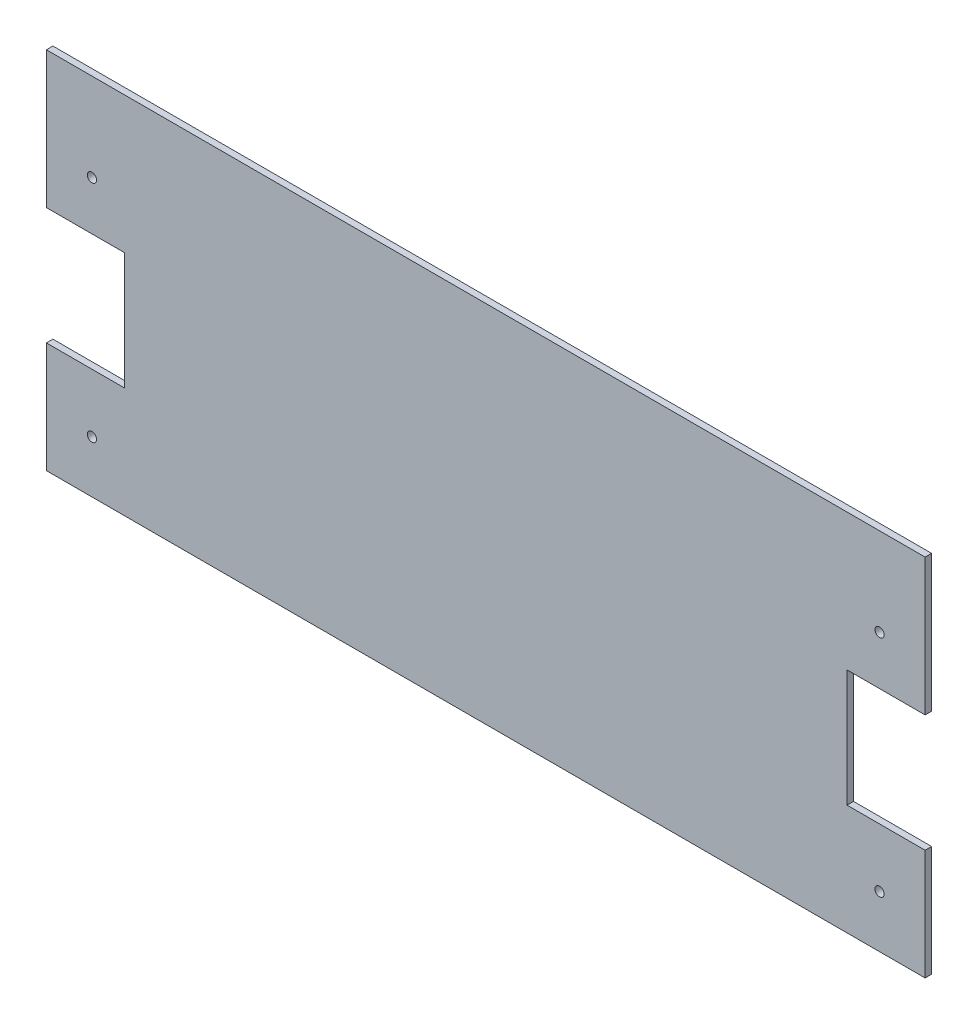
SolidWorks part; units mm, degrees
ref_plane "Front Plane" through (0, 0, 0) normal (0, 0, 1) x (1, 0, 0)
ref_plane "Top Plane" through (0, 0, 0) normal (0, 1, 0) x (1, 0, 0)
ref_plane "Right Plane" through (0, 0, 0) normal (1, 0, 0) x (0, 0, -1)
sketch "Sketch1" plane through (0, 0, 0) normal (0, 0, 1) x (1, 0, 0)
  line L0 (0, 88.9) -> (0, -88.9) construction
  line L1 (-214.3125, -88.9) -> (214.3125, -88.9)
  line L2 (-214.3125, -88.9) -> (-214.3125, 88.9)
  line L3 (-214.3125, 88.9) -> (214.3125, 88.9)
  line L4 (214.3125, -88.9) -> (214.3125, 88.9)
  line L5 (-214.3125, -88.9) -> (214.3125, 88.9) construction
  line L6 (-214.3125, 88.9) -> (214.3125, -88.9) construction
  line L7 (-214.3125, -34.925) -> (-176.2125, -34.925)
  line L8 (-214.3125, -34.925) -> (-214.3125, 22.225)
  line L9 (-214.3125, 22.225) -> (-176.2125, 22.225)
  line L10 (-176.2125, -34.925) -> (-176.2125, 22.225)
  line L11 (214.3125, 22.225) -> (176.2125, 22.225)
  line L12 (176.2125, -34.925) -> (176.2125, 22.225)
  line L13 (214.3125, -34.925) -> (176.2125, -34.925)
  line L14 (214.3125, -34.925) -> (214.3125, 22.225)
  circle A0 centre (-192.0875, 46.0375) radius 2.25
  circle A1 centre (-192.0875, -63.5) radius 2.25
  circle A2 centre (192.0875, -63.5) radius 2.25
  circle A3 centre (192.0875, 46.0375) radius 2.25
  point P0 (0, 0)
  dimension "D3" = 4.5
  dimension "D4" = 4.5
  dimension "D7" = 42.8625
  dimension "D1" = 428.625
  dimension "D2" = 177.8
  dimension "D5" = 22.225
  dimension "D6" = 22.225
  dimension "D8" = 152.4
  dimension "D9" = 66.675
  dimension "D10" = 123.825
  dimension "D11" = 38.1
extrude "Boss-Extrude1" add sketch "Sketch1" against normal blind 3.175 contours L4 L13 L12 L11 L3 L2 L9 L10 L7 L1 A2 A1 A0 A3
